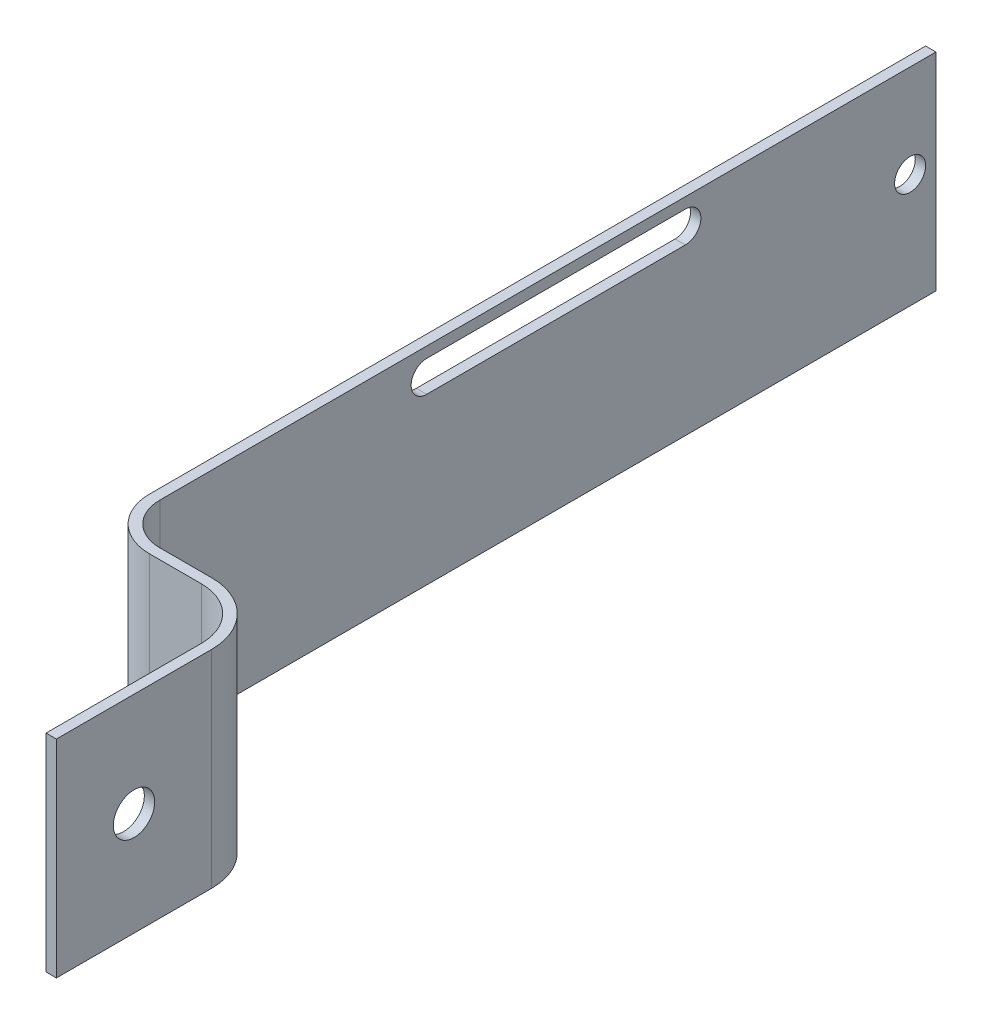
SolidWorks part; units mm, degrees
other "Item de detalhe1"
other "Item de detalhe2"
other "Item de detalhe3" parameters "RD1"=75, "RD2"=15, "RD3"=15, "RD4"=25, "RD5"=20
ref_plane "Front Plane" through (0, 0, 0) normal (0, 0, 1) x (1, 0, 0)
ref_plane "Top Plane" through (0, 0, 0) normal (0, 1, 0) x (1, 0, 0)
ref_plane "Right Plane" through (0, 0, 0) normal (1, 0, 0) x (0, 0, -1)
sketch "Sketch1" plane through (0, 0, 0) normal (0, 1, 0) x (1, 0, 0)
  line L0 (0, 0) -> (0, 15)
  line L1 (-5, 20) -> (-10, 20)
  line L2 (-15, 25) -> (-15, 100)
  arc A0 (0, 15) -> (-5, 20) centre (-5, 15) ccw
  arc A1 (-15, 25) -> (-10, 20) centre (-10, 25) ccw
  dimension "D1" = 5
extrude "Extrude-Thin1" add sketch "Sketch1" along normal blind 20 thin
sketch "Sketch2" plane through (1, 0, 0) normal (1, 0, 0) x (0, 0, -1)
  line L0 (7.5, 0) -> (7.5, 20) construction
  line L1 (0, 0) -> (15, 0) construction
  line L2 (0, 20) -> (15, 20) construction
  circle A0 centre (7.5, 10) radius 2
extrude "Cut-Extrude1" cut sketch "Sketch2" against normal through all
sketch "Sketch3" plane through (-14, 0, 0) normal (1, 0, 0) x (0, 0, -1)
  circle A1 centre (97.5, 11) radius 1.5
extrude "Cut-Extrude2" cut sketch "Sketch3" against normal through all
sketch "Sketch4" plane through (-15, 0, 0) normal (-1, 0, 0) x (0, 0, 1)
  line L0 (-68.2069, 17.4591) -> (-50.7833, 17.4591) construction
  line L1 (-68.2069, 17.4591) -> (-75.7833, 17.4591) construction
  line L2 (-50.7833, 18.9591) -> (-75.7833, 18.9591)
  line L3 (-50.7833, 15.9591) -> (-75.7833, 15.9591)
  arc A1 (-75.7833, 18.9591) -> (-75.7833, 15.9591) centre (-75.7833, 17.4591) ccw
  arc A2 (-50.7833, 15.9591) -> (-50.7833, 18.9591) centre (-50.7833, 17.4591) ccw
extrude "Cut-Extrude3" cut sketch "Sketch4" against normal through all
